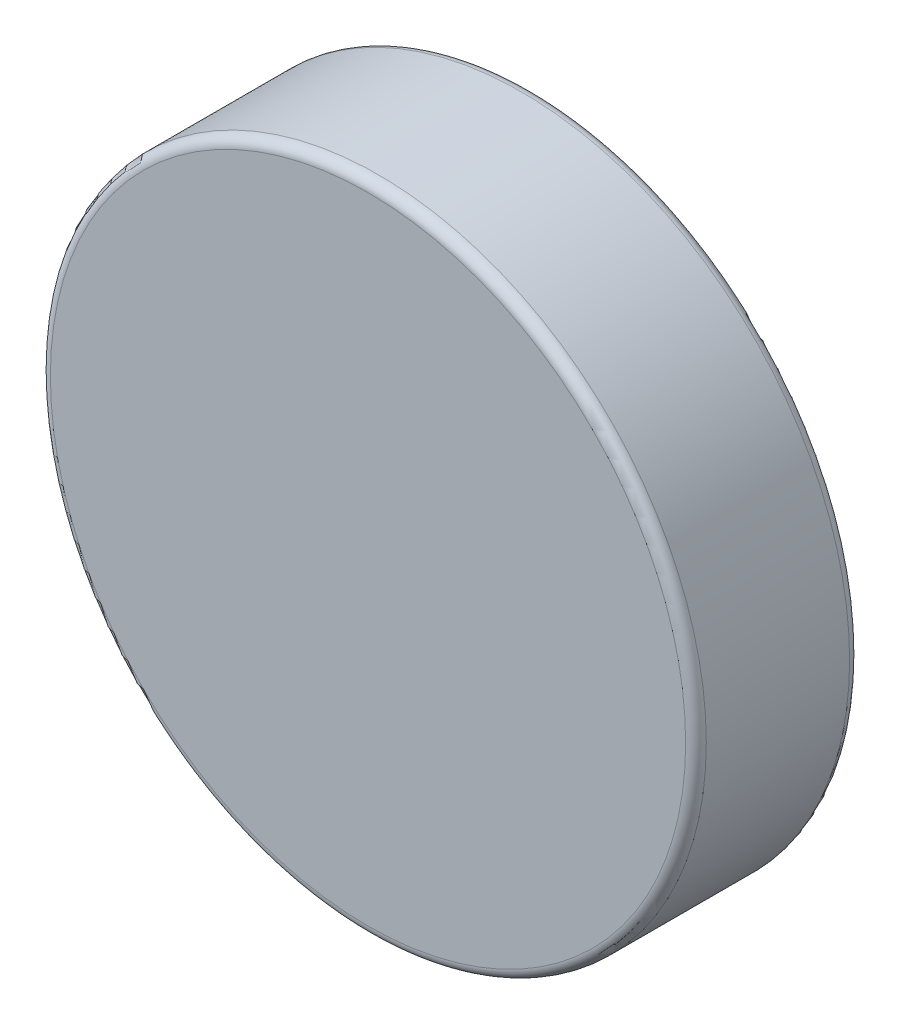
SolidWorks part; units mm, degrees
ref_plane "Front Plane" through (0, 0, 0) normal (0, 0, 1) x (1, 0, 0)
ref_plane "Top Plane" through (0, 0, 0) normal (0, 1, 0) x (1, 0, 0)
ref_plane "Right Plane" through (0, 0, 0) normal (1, 0, 0) x (0, 0, -1)
sketch "Sketch1" plane through (0, 0, 0) normal (0, 1, 0) x (1, 0, 0)
  circle A0 centre (0, 0) radius 4.7625
  dimension "D1" = 9.525
extrude "Boss-Extrude1" [suppressed] add sketch "Sketch1" along normal blind 6.35
fillet "Fillet1" [suppressed] radius 0.25
sketch "Sketch2" plane through (0, 0, 0) normal (0, 0, 1) x (1, 0, 0)
  circle A0 centre (0, 0) radius 3.175
  dimension "D1" = 6.35
extrude "Boss-Extrude2" add sketch "Sketch2" along normal blind 1.5875
fillet "Fillet2" radius 0.1 2 edges at (3.175, 0, 0) (3.175, 0, 1.5875)
